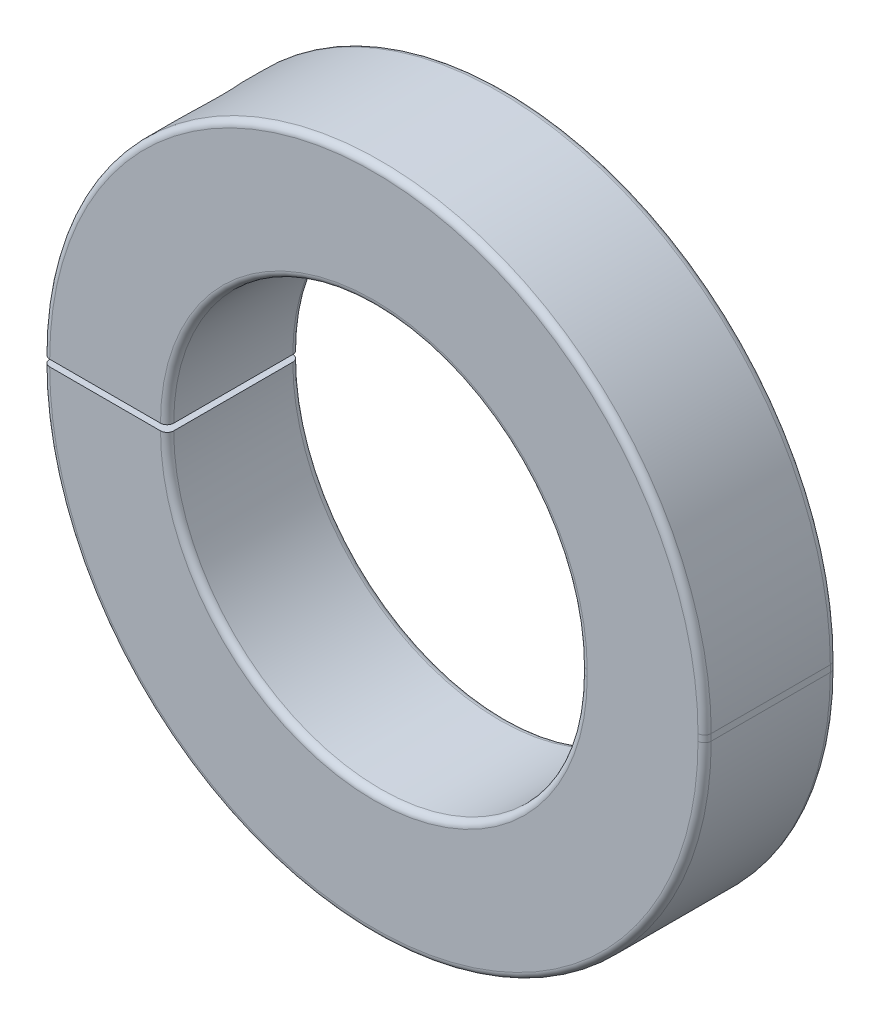
SolidWorks part; units mm, degrees
ref_plane "Front Plane" through (0, 0, 0) normal (0, 0, 1) x (1, 0, 0)
ref_plane "Top Plane" through (0, 0, 0) normal (0, 1, 0) x (1, 0, 0)
ref_plane "Right Plane" through (0, 0, 0) normal (1, 0, 0) x (0, 0, -1)
sketch "Sketch1" plane through (0, 0, 0) normal (0, 0, 1) x (1, 0, 0)
  line L0 (-31.75, 0) -> (-19.8438, 0) construction
  line L1 (-31.75, 0.3175) -> (-19.8438, 0.3175)
  line L2 (-31.75, -0.3175) -> (-19.8438, -0.3175)
  line L3 (19.8438, 0.3175) -> (31.75, 0.3175) construction
  line L4 (19.8438, -0.3175) -> (31.75, -0.3175) construction
  line L5 (0, 0) -> (0, 31.75) construction
  line L6 (31.75, 0.3175) -> (31.75, -0.3175)
  line L7 (19.8438, 0.3175) -> (19.8438, -0.3175)
  circle A0 centre (0, 0) radius 31.75 construction
  circle A1 centre (0, 0) radius 19.8438 construction
  arc A2 (-31.75, 0.3175) -> (31.75, 0.3175) centre (0, 0.3175) cw
  arc A3 (-31.75, -0.3175) -> (31.75, -0.3175) centre (0, -0.3175) ccw
  arc A4 (-19.8438, 0.3175) -> (19.8438, 0.3175) centre (0, 0.3175) cw
  arc A5 (-19.8438, -0.3175) -> (19.8438, -0.3175) centre (0, -0.3175) ccw
  point P4 (31.75, 0)
  dimension "Bore Dia" = 39.6875
  dimension "OD" = 63.5
  dimension "Separation" = 0.635
extrude "Extrude1" add sketch "Sketch1" along normal mid plane 12.7
sketch "Sketch4" plane through (0, 0, 0) normal (0, 0, 1) x (1, 0, 0)
  line L0 (-25.7969, 32.0675) -> (-21.0344, 32.0675)
  line L1 (-21.0344, 32.0675) -> (-21.0344, 3.4925)
  line L2 (-21.0344, 3.4925) -> (-22.6219, 3.4925)
  line L3 (-22.6219, 3.4925) -> (-22.6219, -32.0675)
  line L4 (-22.6219, -32.0675) -> (-25.7969, -32.0675)
  line L5 (-25.7969, -32.0675) -> (-25.7969, 32.0675)
  line L6 (-21.0344, 9.8425) -> (-30.5594, 9.8425) construction
  line L7 (-25.7969, 32.0675) -> (-25.7969, 34.6075) construction
  line L8 (-21.0344, 32.0675) -> (0, 32.0675) construction
  line L9 (0, -32.0675) -> (-22.6219, -32.0675) construction
  line L10 (-31.75, 0) -> (-19.8438, 0) construction
  line L11 (-31.75, 0.3175) -> (-19.8438, 0.3175) construction
  circle A0 centre (0, 0) radius 31.75 construction
  arc A1 (31.75, 0.3175) -> (-31.75, 0.3175) centre (0, 0.3175) ccw construction
  circle A2 centre (0, 0) radius 19.8438 construction
  arc A3 (-31.75, -0.3175) -> (31.75, -0.3175) centre (0, -0.3175) ccw construction
  point P13 (-25.7969, 0)
  point P19 (-25.7969, 0)
  point P20 (-25.7969, 9.8425)
  dimension "D1" = 6.35
  dimension "D2" = 11.9062
  dimension "D3" = 3.175
  dimension "D4" = 9.525
  dimension "D5" = 2.54
  dimension "Screw Dia" = 6.35
revolve "Cut-Revolve1" cut sketch "Sketch4" angle 360 about L5
sketch "Sketch6" plane through (0, 0, 0) normal (0, 0, 1) x (1, 0, 0)
  line L0 (-25.7969, 9.8425) -> (-21.0344, 9.8425)
  line L1 (-21.0344, 9.8425) -> (-30.5594, 9.8425) construction
  line L2 (-21.0344, 9.8425) -> (-21.0344, 3.4925)
  line L3 (-21.0344, 3.4925) -> (-22.6219, 3.4925)
  line L4 (-22.6219, 3.4925) -> (-22.6219, -9.2075)
  line L5 (-22.6219, 3.4925) -> (-22.6219, -32.0675) construction
  line L6 (-22.6219, -9.2075) -> (-25.7969, -9.2075)
  line L7 (-25.7969, -32.0675) -> (-25.7969, 32.0675) construction
  line L8 (-25.7969, -9.2075) -> (-25.7969, 9.8425)
  line L9 (-22.6219, -9.2075) -> (-28.9719, -9.2075) construction
  dimension "Head Ht" = 6.35
  dimension "Screw Lg" = 19.05
revolve "Revolve1" add sketch "Sketch6" angle 360 about L8
sketch "Sketch7" plane through (0, 9.8425, 0) normal (0, 1, 0) x (-1, 0, 0)
  line L1 (25.7969, -2.9329) -> (28.3369, -1.4665)
  line L2 (28.3369, -1.4665) -> (28.3369, 1.4665)
  line L3 (28.3369, 1.4665) -> (25.7969, 2.9329)
  line L4 (25.7969, 2.9329) -> (23.2569, 1.4665)
  line L5 (23.2569, 1.4665) -> (23.2569, -1.4665)
  line L6 (23.2569, -1.4665) -> (25.7969, -2.9329)
  circle A0 centre (25.7969, 0) radius 2.54 construction
  dimension "D1" = 5.08
extrude "Cut-Extrude2" cut sketch "Sketch7" against normal blind 3.175
fillet "Fillet1" radius 0.635 12 edges at (0, 20.1612, -6.35) (0, 20.1612, 6.35) (0, 32.0675, -6.35) (0, 32.0675, 6.35) (0, -32.0675, -6.35) (0, -32.0675, 6.35) (31.75, 0, -6.35) (31.75, 0, 6.35) (0, -20.1612, -6.35) (19.8438, 0, -6.35) (0, -20.1612, 6.35) (19.8438, 0, 6.35)
chamfer "Chamfer2" distance 0.254 angle 45 1 edges at (-21.0344, 9.8425, 0)
equation "\"D1@Sketch4\" = \"Screw Dia@Sketch4\""
equation "\"D4@Sketch4\" = \"Screw Dia@Sketch4\"*1.5"
equation "\"D1@Sketch7\" = \"Screw Dia@Sketch4\"*.8"
equation "\"D1@Cut-Extrude2\" = \"Head Ht@Sketch6\"/2"
equation "\"D3@Sketch4\" = \"D1@Sketch4\"*.5"
equation "\"D1@Fillet1\" = \"Width@Extrude1\"*.05"
equation "\"Screw Lg@Sketch6\" = \"Head Ht@Sketch6\"*3"
equation "\"Separation@Sketch1\" = \"OD@Sketch1\"*.01"
